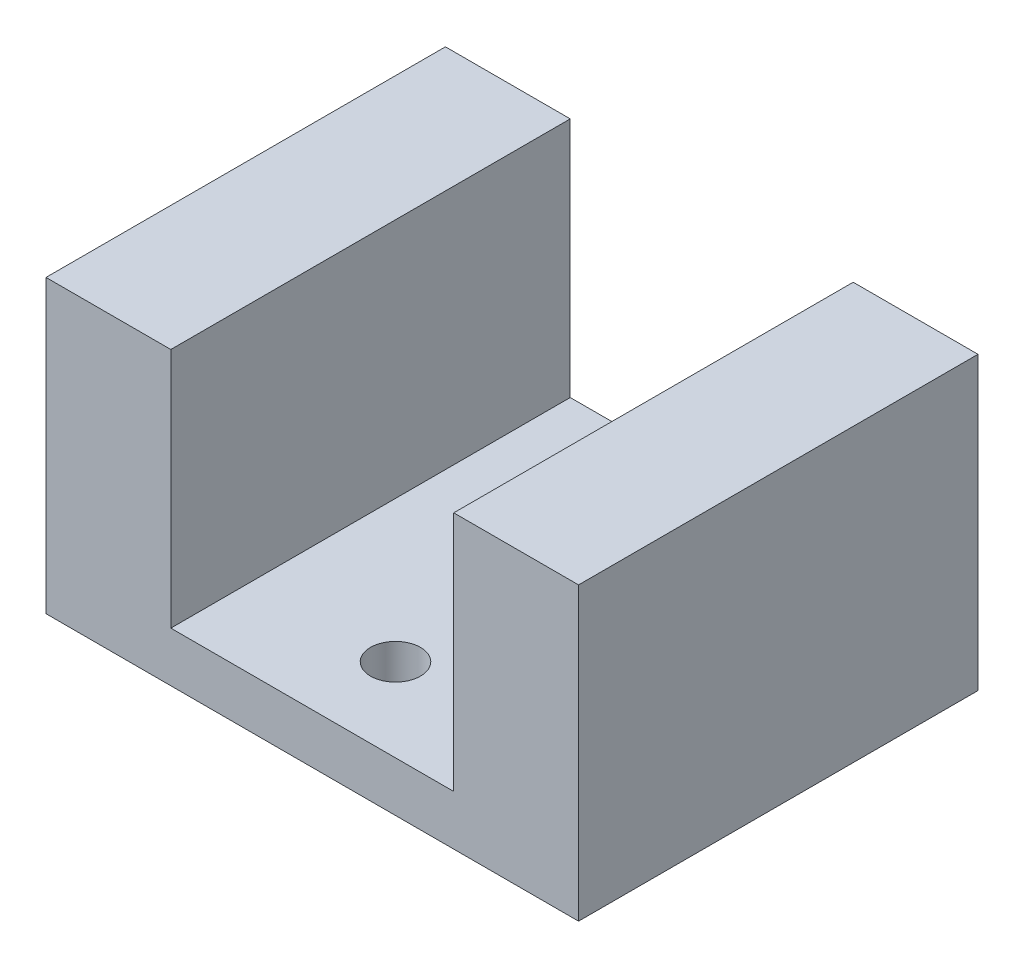
SolidWorks part; units mm, degrees
ref_plane "Front Plane" through (0, 0, 0) normal (0, 0, 1) x (1, 0, 0)
ref_plane "Top Plane" through (0, 0, 0) normal (0, 1, 0) x (1, 0, 0)
ref_plane "Right Plane" through (0, 0, 0) normal (1, 0, 0) x (0, 0, -1)
sketch "Sketch3" plane through (0, 0, 0) normal (0, 0, 1) x (1, 0, 0)
  line L0 (-16, 0) -> (16, 0)
  line L1 (16, 0) -> (16, 17.5)
  line L2 (16, 17.5) -> (8.5, 17.5)
  line L3 (8.5, 17.5) -> (8.5, 3)
  line L4 (8.5, 3) -> (-8.5, 3)
  line L5 (-8.5, 3) -> (-8.5, 17.5)
  line L6 (-8.5, 17.5) -> (-16, 17.5)
  line L7 (-16, 17.5) -> (-16, 0)
  point P4 (0, 0)
  dimension "D1" = 32
  dimension "D2" = 3
  dimension "D3" = 7.5
  dimension "D4" = 17.5
extrude "Boss-Extrude1" add sketch "Sketch3" along normal blind 24
sketch "Sketch4" plane through (0, 3, 0) normal (0, 1, 0) x (1, 0, 0)
  line L0 (8.5, 0) -> (-8.5, 0) construction
  circle A0 centre (0, -5) radius 1.5
  circle A1 centre (0, -12) radius 2.05
  circle A2 centre (0, -19) radius 1.5
  point P8 (0, 0)
  dimension "D1" = 3
  dimension "D2" = 4.1
  dimension "D3" = 5
  dimension "D4" = 12
  dimension "D5" = 19
extrude "Cut-Extrude1" cut sketch "Sketch4" against normal up to next
